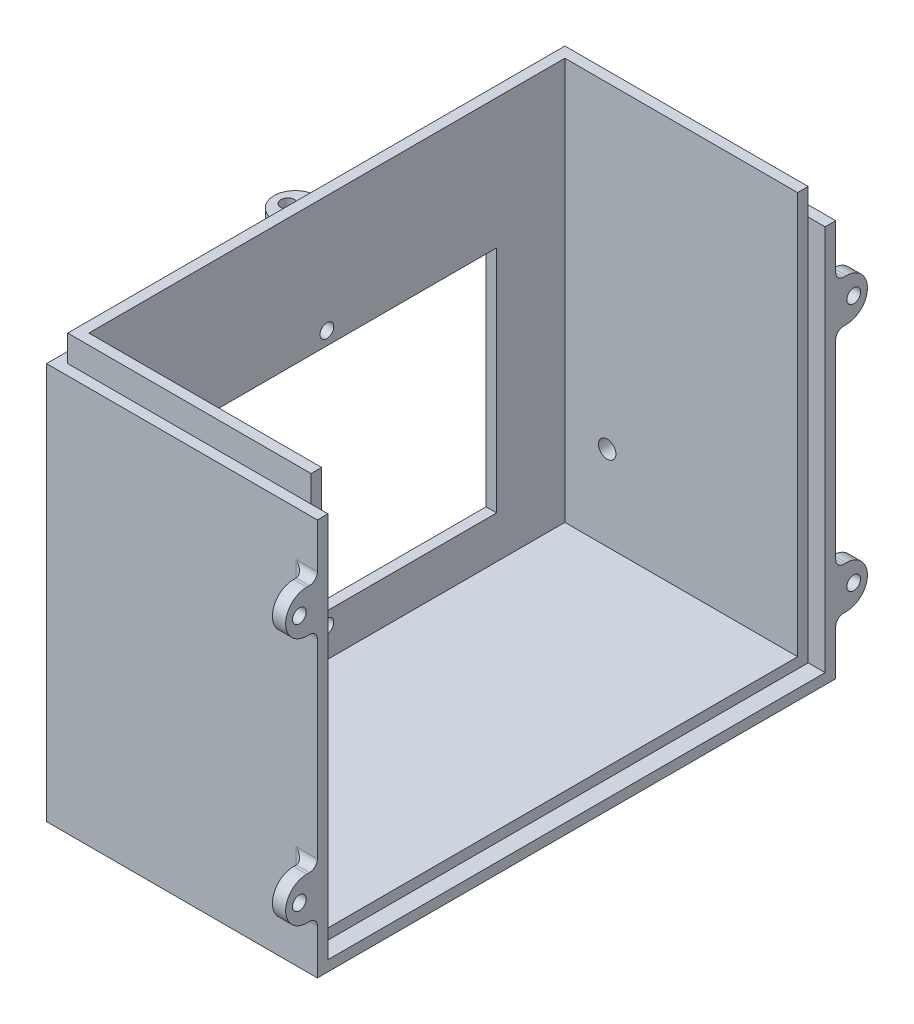
SolidWorks part; units mm, degrees
ref_plane "Front Plane" through (0, 0, 0) normal (0, 0, 1) x (1, 0, 0)
ref_plane "Top Plane" through (0, 0, 0) normal (0, 1, 0) x (1, 0, 0)
ref_plane "Right Plane" through (0, 0, 0) normal (1, 0, 0) x (0, 0, -1)
sketch "Sketch1" plane through (0, 0, 0) normal (0, 1, 0) x (1, 0, 0)
  line L1 (-26.5, 49) -> (26.5, 49)
  line L2 (-26.5, 49) -> (-26.5, -49)
  line L3 (-26.5, -49) -> (26.5, -49)
  line L4 (26.5, 49) -> (26.5, -49)
  line L5 (-26.5, 49) -> (26.5, -49) construction
  line L6 (-26.5, -49) -> (26.5, 49) construction
  point P0 (0, 0)
  dimension "D1" = 53
  dimension "D2" = 98
extrude "Boss-Extrude1" add sketch "Sketch1" along normal blind 80
sketch "Sketch2" plane through (26.5, 0, 0) normal (1, 0, 0) x (0, 0, -1)
  line L0 (-49, 80) -> (49, 80) construction
  line L1 (-45, 80) -> (45, 80)
  line L2 (-45, 80) -> (-45, 4)
  line L3 (-45, 4) -> (45, 4)
  line L4 (45, 80) -> (45, 4)
  line L5 (-49, 80) -> (-49, 0) construction
  line L6 (49, 80) -> (49, 0) construction
  line L7 (-49, 0) -> (49, 0) construction
  dimension "D1" = 4
  dimension "D2" = 4
  dimension "D3" = 4
extrude "Cut-Extrude1" cut sketch "Sketch2" against normal blind 49
sketch "Sketch3" plane through (0, 80, 0) normal (0, 1, 0) x (1, 0, 0)
  line L0 (-26.5, 49) -> (-26.5, -49) construction
  line L1 (26.5, -49) -> (-26.5, -49)
  line L2 (26.5, -49) -> (26.5, -47)
  line L3 (26.5, -47) -> (-26.5, -47)
  line L4 (-26.5, -49) -> (-26.5, -47)
  line L5 (26.5, 49) -> (-26.5, 49) construction
  line L6 (-26.5, -47) -> (-24.5, -47)
  line L7 (-26.5, -47) -> (-26.5, 49)
  line L8 (-26.5, 49) -> (-24.5, 49)
  line L9 (-24.5, -47) -> (-24.5, 49)
  line L10 (26.5, 45) -> (26.5, 49) construction
  line L11 (-24.5, 49) -> (26.5, 49)
  line L12 (-24.5, 49) -> (-24.5, 47)
  line L13 (-24.5, 47) -> (26.5, 47)
  line L14 (26.5, 49) -> (26.5, 47)
  line M6 (26.5, 45) -> (26.5, 49)
  line M7 (26.5, 49) -> (-26.5, 49)
  line M8 (-26.5, 49) -> (-26.5, -49)
  line M9 (-26.5, -49) -> (26.5, -49)
  line M10 (26.5, -49) -> (26.5, -45)
  dimension "D1" = 2
  dimension "D2" = 2
extrude "Cut-Extrude2" cut sketch "Sketch3" against normal blind 5 contours L3 M10 M8 M9 | L3 L9 M7 M8 | L9 L13 M6 M7
sketch "Sketch5" plane through (26.5, 0, 0) normal (1, 0, 0) x (0, 0, -1)
  line L0 (-45, 4) -> (45, 4) construction
  line L1 (-47, 80) -> (-45, 80)
  line L2 (-47, 80) -> (-47, 4)
  line L3 (-47, 4) -> (-45, 4)
  line L4 (-45, 80) -> (-45, 4)
  line L5 (-45, 80) -> (-45, 4) construction
  line L7 (47, 80) -> (45, 80)
  line L8 (47, 80) -> (47, 4)
  line L9 (47, 4) -> (45, 4)
  line L10 (45, 80) -> (45, 4)
  line L11 (-47, 4) -> (47, 4)
  line L12 (-47, 4) -> (-47, 2)
  line L13 (-47, 2) -> (47, 2)
  line L14 (47, 4) -> (47, 2)
  line M10 (47, 75) -> (47, 80)
  line M11 (47, 80) -> (45, 80)
  line M12 (45, 80) -> (45, 4)
  line M13 (45, 4) -> (-45, 4)
  dimension "D1" = 2
extrude "Cut-Extrude3" cut sketch "Sketch5" against normal blind 5 contours L14 L9 L3 L12 L13 M13 | L9 L8 M10 M11 M12
sketch "Sketch6" plane through (26.5, 0, 0) normal (1, 0, 0) x (0, 0, -1)
  line L1 (-49, 75) -> (49, 75)
  line L2 (-49, 75) -> (-49, 0)
  line L3 (-49, 0) -> (49, 0)
  line L4 (49, 75) -> (49, 0)
  line L5 (-47, 75) -> (47, 75)
  line L6 (-47, 75) -> (-47, 2)
  line L7 (-47, 2) -> (47, 2)
  line L8 (47, 75) -> (47, 2)
  line M1 (47, 2) -> (-47, 2)
  line M2 (-47, 2) -> (-47, 75)
  line M3 (-47, 75) -> (-49, 75)
  line M4 (-49, 75) -> (-49, 0)
  line M5 (-49, 0) -> (49, 0)
  line M6 (49, 0) -> (49, 75)
  line M7 (49, 75) -> (47, 75)
  line M8 (47, 75) -> (47, 2)
extrude "Cut-Extrude4" cut sketch "Sketch6" against normal blind 1.8 contours M8 M1 M2 M3 M4 M5 M6 M7
sketch "Sketch8" plane through (24.7, 0, 0) normal (1, 0, 0) x (0, 0, -1)
  line L0 (-49, 75) -> (-49, 0) construction
  line L1 (-49, 10) -> (-51, 10)
  line L2 (-49, 10) -> (-49, 18)
  line L3 (-49, 18) -> (-51, 18)
  line L5 (-49, 0) -> (49, 0) construction
  line L6 (-49, 37.5) -> (-32.7041, 37.5) construction
  line L7 (-49, 65) -> (-49, 57)
  line L8 (-49, 65) -> (-51, 65)
  line L9 (-49, 57) -> (-51, 57)
  line L10 (0, 0) -> (0, 27.8647) construction
  line L11 (49, 10) -> (49, 18)
  line L12 (49, 10) -> (51, 10)
  line L13 (49, 18) -> (51, 18)
  line L14 (49, 65) -> (51, 65)
  line L15 (49, 57) -> (51, 57)
  line L16 (49, 65) -> (49, 57)
  arc A0 (-51, 18) -> (-51, 10) centre (-51, 14) ccw
  circle A1 centre (-52.4, 14) radius 1.3
  circle A2 centre (-52.4, 61) radius 1.3
  arc A3 (-51, 57) -> (-51, 65) centre (-51, 61) cw
  arc A4 (51, 18) -> (51, 10) centre (51, 14) cw
  circle A5 centre (52.4, 14) radius 1.3
  circle A6 centre (52.4, 61) radius 1.3
  arc A7 (51, 57) -> (51, 65) centre (51, 61) ccw
  dimension "D4" = 2.6
  dimension "D1" = 2
  dimension "D2" = 8
  dimension "D3" = 10
  dimension "D5" = 3.4
extrude "Boss-Extrude3" add sketch "Sketch8" against normal blind 2.5
fillet "Fillet2" radius 1.5 12 edges at (23.45, 65, -49) (22.2, 61, -49) (23.45, 57, -49) (23.45, 18, -49) (22.2, 14, -49) (23.45, 10, -49) (23.45, 10, 49) (23.45, 57, 49) (22.2, 14, 49) (23.45, 18, 49) (22.2, 61, 49) (23.45, 65, 49)
sketch "Sketch9" plane through (0, 75, 0) normal (0, 1, 0) x (1, 0, 0)
  line L0 (-26.5, 49) -> (-26.5, -49) construction
  line L1 (-26.5, 4) -> (-28.5, 4)
  line L2 (-26.5, 4) -> (-26.5, -4)
  line L3 (-26.5, -4) -> (-28.5, -4)
  line L5 (24.7, 49) -> (-26.5, 49) construction
  arc A0 (-28.5, 4) -> (-28.5, -4) centre (-28.5, 0) ccw
  circle A1 centre (-29.9, 0) radius 1.3
  dimension "D4" = 2.6
  dimension "D5" = 3.4
  dimension "D1" = 2
  dimension "D2" = 8
  dimension "D3" = 45
extrude "Boss-Extrude4" add sketch "Sketch9" against normal blind 2.5
fillet "Fillet4" radius 1.5 3 edges at (-26.5, 73.75, -4) (-26.5, 72.5, 0) (-26.5, 73.75, 4)
sketch "Sketch14" plane through (-26.5, 0, 0) normal (-1, 0, 0) x (0, 0, 1)
  line L0 (-49, 0) -> (49, 0) construction
  line L1 (-32.1, 55.4) -> (32.1, 55.4)
  line L2 (-32.1, 55.4) -> (-32.1, 12)
  line L3 (-32.1, 12) -> (32.1, 12)
  line L4 (32.1, 55.4) -> (32.1, 12)
  line L5 (-32.1, 55.4) -> (32.1, 12) construction
  line L6 (-32.1, 12) -> (32.1, 55.4) construction
  line L7 (-49, 75) -> (-49, 0) construction
  point P0 (0, 33.7)
  dimension "D1" = 64.2
  dimension "D2" = 43.4
  dimension "D3" = 12
  dimension "D4" = 16.9
extrude "Cut-Extrude6" cut sketch "Sketch14" against normal up to next
sketch "Sketch15" plane through (-26.5, 0, 0) normal (-1, 0, 0) x (0, 0, 1)
  line L0 (-32.1, 55.4) -> (-32.1, 12) construction
  line L1 (-37.1, 60.4) -> (37.1, 60.4)
  line L2 (-37.1, 60.4) -> (-37.1, 7)
  line L3 (-37.1, 7) -> (37.1, 7)
  line L4 (37.1, 60.4) -> (37.1, 7)
  line L5 (-37.1, 60.4) -> (37.1, 7) construction
  line L6 (-37.1, 7) -> (37.1, 60.4) construction
  line L7 (32.1, 55.4) -> (-32.1, 55.4) construction
  line L8 (-32.1, 12) -> (32.1, 12) construction
  line L9 (32.1, 12) -> (32.1, 55.4) construction
  point P0 (0, 33.7)
  dimension "D1" = 5
  dimension "D2" = 5
  dimension "D3" = 5
  dimension "D4" = 5
extrude "Cut-Extrude7" cut sketch "Sketch15" against normal blind 2
sketch "Sketch16" plane through (-24.5, 0, 0) normal (-1, 0, 0) x (0, 0, 1)
  line L0 (-32.1, 55.4) -> (32.1, 55.4) construction
  line L1 (32.1, 12) -> (-32.1, 12) construction
  circle A0 centre (0, 57.9) radius 1.3
  circle A1 centre (0, 9.5) radius 1.3
  dimension "D1" = 2.6
  dimension "D2" = 2.6
  dimension "D3" = 2.5
  dimension "D4" = 2.5
extrude "Cut-Extrude8" cut sketch "Sketch16" against normal up to next
sketch "Sketch29" plane through (0, 0, -49) normal (0, 0, -1) x (-1, 0, 0)
  line L0 (26.5, 75) -> (26.5, 0) construction
  line L1 (-24.7, 75) -> (26.5, 75) construction
  circle A0 centre (14.5, 20) radius 1.65
  dimension "D1" = 3.3
  dimension "D2" = 12
  dimension "D3" = 55
extrude "Cut-Extrude12" cut sketch "Sketch29" against normal up to next
